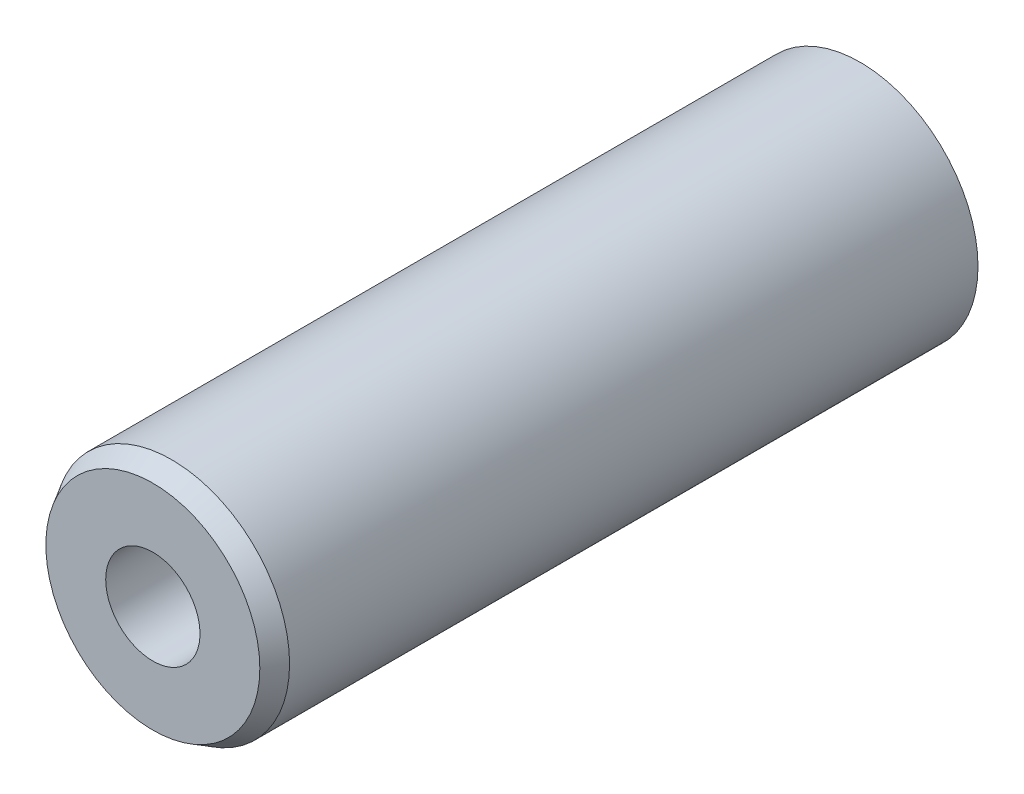
SolidWorks part; units mm, degrees
ref_plane "Front Plane" through (0, 0, 0) normal (0, 0, 1) x (1, 0, 0)
ref_plane "Top Plane" through (0, 0, 0) normal (0, 1, 0) x (1, 0, 0)
ref_plane "Right Plane" through (0, 0, 0) normal (1, 0, 0) x (0, 0, -1)
sketch "Sketch1" plane through (0, 0, 0) normal (0, 0, 1) x (1, 0, 0)
  circle A0 centre (0, 0) radius 2.5
  dimension "D1" = 5
extrude "Boss-Extrude1" add sketch "Sketch1" along normal blind 15
cosmetic thread "Cosmetic Thread2" parameters "D1"=4, "D2"=4.11
sketch "Sketch2" plane through (0, 0, 0) normal (0, 0, -1) x (-1, 0, 0)
  circle A0 centre (0, 0) radius 1
  dimension "D1" = 2
extrude "Cut-Extrude1" cut sketch "Sketch2" against normal through all
hole_wizard "Tap Drill for M3x0.5 Tap1" positions "Sketch4" profile "Sketch3" hole size "M3x0.5" standard "Ansi Metric"
sketch "Sketch4" plane through (0, 0, 0) normal (0, 0, -1) x (-1, 0, 0)
  point P0 (0, 0)
sketch "Sketch3" plane through (0, 0, 0) normal (1, 0, 0) x (0, 1, 0)
  line L0 (0, 0) -> (0, 11.7511)
  line L1 (0, 11.7511) -> (1.25, 11)
  line L2 (1.25, 11) -> (1.25, 0)
  line L5 (1.25, 0) -> (0, 0)
  line L10 (0, 11.7511) -> (-1.25, 11) construction
  line L11 (0, -6.35) -> (0, 107.95) construction
  dimension "Hole Dia." = 2.5
  dimension "Hole Depth" = 11
  dimension "Drill Angle" = 118
cosmetic thread "Cosmetic Thread3" parameters "D1"=10, "D2"=3
chamfer "Chamfer1" distance 0.4 angle 30 1 edges at (2.5, 0, 15)
chamfer "Chamfer2" distance 0.4 angle 60 1 edges at (-1.25, 0, 0)
